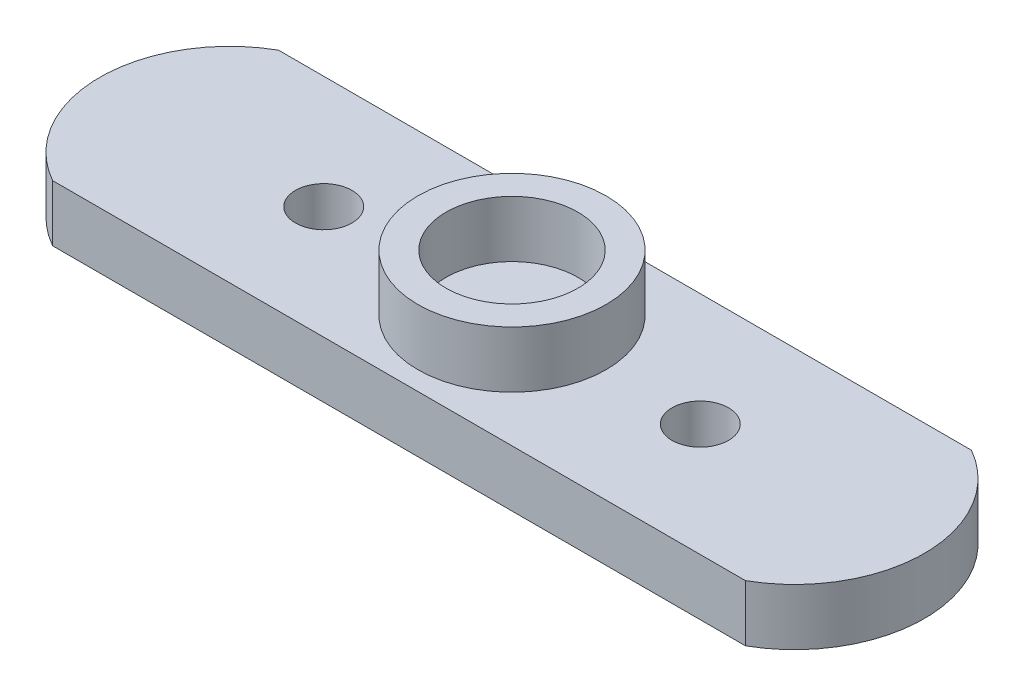
SolidWorks part; units mm, degrees
material "ABS"
ref_plane "Front Plane" through (0, 0, 0) normal (0, 0, 1) x (1, 0, 0)
ref_plane "Top Plane" through (0, 0, 0) normal (0, 1, 0) x (1, 0, 0)
ref_plane "Right Plane" through (0, 0, 0) normal (1, 0, 0) x (0, 0, -1)
ref_plane "Top Plane1" through (0, 3, 0) normal (0, 1, 0) x (1, 0, 0)
sketch "Sketch1" plane through (0, 0, 0) normal (0, 1, 0) x (1, 0, 0)
  line L0 (-18.4, 6) -> (18.4, -6) construction
  line L1 (-18.4, 6) -> (18.4, 6)
  line L2 (-10, 0) -> (10, 0) construction
  line L3 (-18.4, -6) -> (18.4, -6)
  line L5 (-21.9, 6) -> (-21.9, -6) construction
  line L6 (21.9, 6) -> (21.9, -6) construction
  arc A1 (-18.4, -6) -> (-18.4, 6) centre (-15.0071, 0) cw
  arc A2 (18.4, -6) -> (18.4, 6) centre (15.0071, 0) ccw
  circle A3 centre (10, 0) radius 1.5025
  circle A4 centre (-10, 0) radius 1.5025
  dimension "D6" = 3.005
  dimension "D7" = 6.8929
  dimension "D1" = 36.8
  dimension "D2" = 12
  dimension "D4" = 43.8
  dimension "D5" = 20
  dimension "D9" = 3.5
  dimension "D10" = 3.5
extrude "Boss-Extrude1" add sketch "Sketch1" along normal blind 3
sketch "Sketch2" plane through (0, 3, 0) normal (0, 1, 0) x (1, 0, 0)
  circle A0 centre (0, 0) radius 5
  circle A1 centre (0, 0) radius 3.5025
  dimension "D1" = 10
  dimension "D2" = 7.005
extrude "Boss-Extrude2" add sketch "Sketch2" along normal blind 3
sketch "Sketch3" plane through (0, 3, 0) normal (0, 1, 0) x (1, 0, 0)
  point P0 (0, 0)
